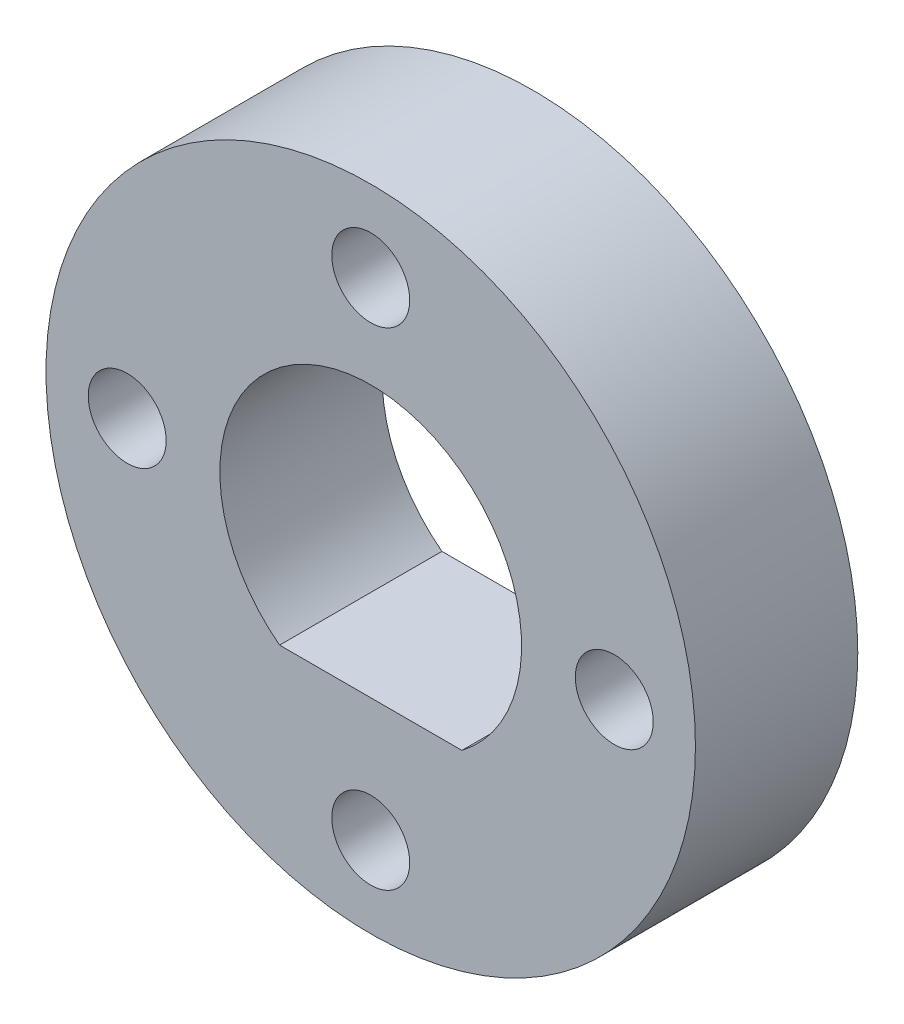
SolidWorks part; units mm, degrees
ref_plane "Front Plane" through (0, 0, 0) normal (0, 0, 1) x (1, 0, 0)
ref_plane "Top Plane" through (0, 0, 0) normal (0, 1, 0) x (1, 0, 0)
ref_plane "Right Plane" through (0, 0, 0) normal (1, 0, 0) x (0, 0, -1)
sketch "Sketch1" plane through (0, 0, 0) normal (0, 0, 1) x (1, 0, 0)
  line L0 (-1.7826, -2.3508) -> (1.7826, -2.3508)
  circle A0 centre (0, 0) radius 6.35
  circle A1 centre (0, 0) radius 4.7625 construction
  arc A2 (1.7826, -2.3508) -> (-1.7826, -2.3508) centre (0, 0) ccw
  circle A3 centre (0, 4.7625) radius 0.762
  circle A4 centre (4.7625, 0) radius 0.762
  circle A5 centre (0, -4.7625) radius 0.762
  circle A6 centre (-4.7625, 0) radius 0.762
  dimension "D1" = 12.7
  dimension "D2" = 9.525
  dimension "D3" = 5.9004
  dimension "D5" = 1.524
  dimension "D4" = 5.301
  dimension "D6" = 4
extrude "Boss-Extrude1" add sketch "Sketch1" along normal blind 3.175
